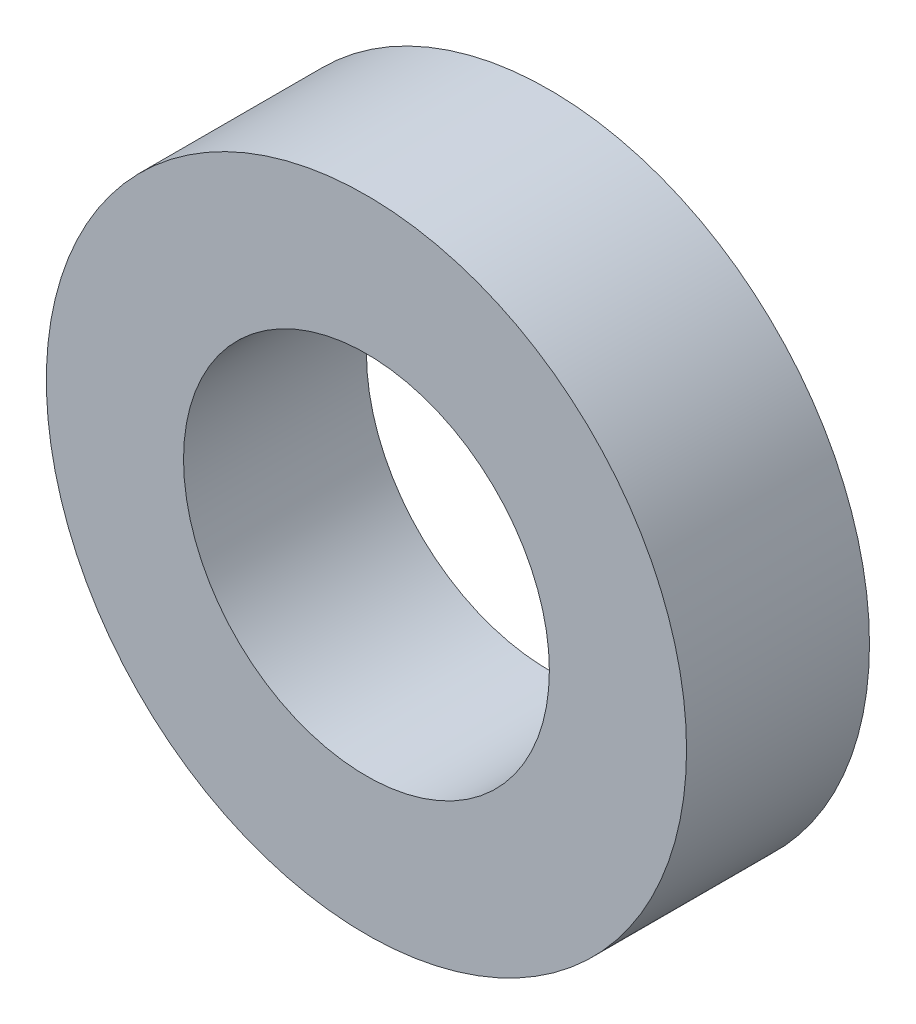
SolidWorks part; units mm, degrees
ref_plane "前视基准面" through (0, 0, 0) normal (0, 0, 1) x (1, 0, 0)
ref_plane "上视基准面" through (0, 0, 0) normal (0, 1, 0) x (1, 0, 0)
ref_plane "右视基准面" through (0, 0, 0) normal (1, 0, 0) x (0, 0, -1)
sketch "草图1" plane through (0, 0, 0) normal (0, 0, 1) x (1, 0, 0)
  circle A0 centre (0, 0) radius 7
  circle A1 centre (0, 0) radius 4
  dimension "D1" = 14
  dimension "D2" = 8
extrude "凸台-拉伸1" add sketch "草图1" along normal mid plane 4
